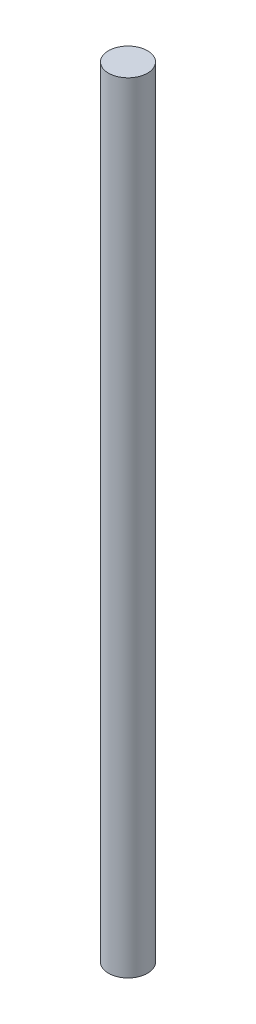
SolidWorks part; units mm, degrees
ref_plane "Front Plane" through (0, 0, 0) normal (0, 0, 1) x (1, 0, 0)
ref_plane "Top Plane" through (0, 0, 0) normal (0, 1, 0) x (1, 0, 0)
ref_plane "Right Plane" through (0, 0, 0) normal (1, 0, 0) x (0, 0, -1)
sketch "Sketch1" plane through (0, 0, 0) normal (0, 1, 0) x (1, 0, 0)
  circle A0 centre (0, 0) radius 3.175
  dimension "D1" = 6.35
extrude "Boss-Extrude1" add sketch "Sketch1" along normal blind 127
